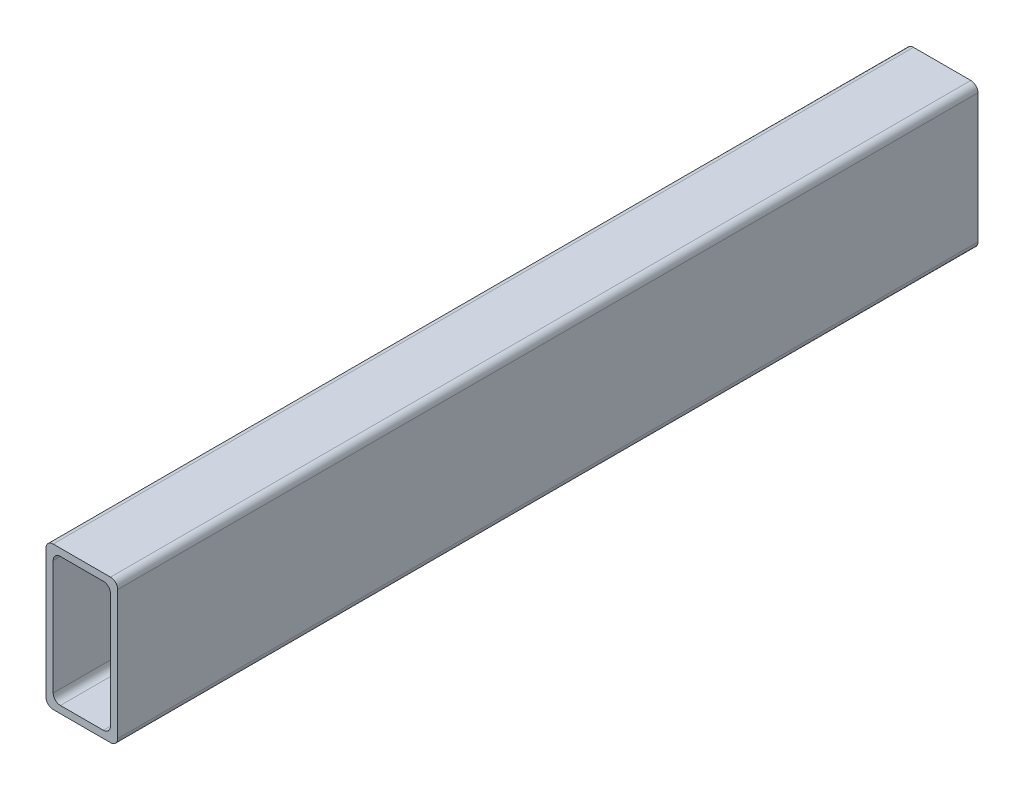
SolidWorks part; units mm, degrees
ref_plane "Спереди" through (0, 0, 0) normal (0, 0, 1) x (1, 0, 0)
ref_plane "Сверху" through (0, 0, 0) normal (0, 1, 0) x (1, 0, 0)
ref_plane "Справа" through (0, 0, 0) normal (1, 0, 0) x (0, 0, -1)
sketch "Эскиз1" plane through (0, 0, 0) normal (0, 0, 1) x (1, 0, 0)
  line L16 (-10, 50) -> (10, 50)
  line L17 (12.5, 47.5) -> (12.5, 2.5)
  line L18 (10, 0) -> (-10, 0)
  line L19 (-12.5, 2.5) -> (-12.5, 47.5)
  line L20 (-7.5, 47.5) -> (7.5, 47.5)
  line L21 (10, 45) -> (10, 5)
  line L22 (7.5, 2.5) -> (-7.5, 2.5)
  line L23 (-10, 5) -> (-10, 45)
  arc A16 (12.5, 47.5) -> (10, 50) centre (10, 47.5) ccw
  arc A17 (10, 0) -> (12.5, 2.5) centre (10, 2.5) ccw
  arc A18 (-12.5, 2.5) -> (-10, 0) centre (-10, 2.5) ccw
  arc A19 (-10, 50) -> (-12.5, 47.5) centre (-10, 47.5) ccw
  arc A20 (10, 45) -> (7.5, 47.5) centre (7.5, 45) ccw
  arc A21 (7.5, 2.5) -> (10, 5) centre (7.5, 5) ccw
  arc A22 (-10, 5) -> (-7.5, 2.5) centre (-7.5, 5) ccw
  arc A23 (-7.5, 47.5) -> (-10, 45) centre (-7.5, 45) ccw
extrude "Бобышка-Вытянуть1" add sketch "Эскиз1" against normal blind 300
